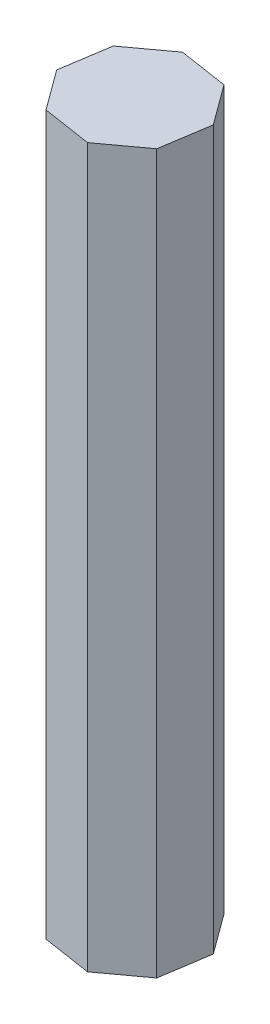
SolidWorks part; units mm, degrees
ref_plane "Front Plane" through (0, 0, 0) normal (0, 0, 1) x (1, 0, 0)
ref_plane "Top Plane" through (0, 0, 0) normal (0, 1, 0) x (1, 0, 0)
ref_plane "Right Plane" through (0, 0, 0) normal (1, 0, 0) x (0, 0, -1)
sketch "Sketch1" plane through (0, 0, 0) normal (0, 1, 0) x (1, 0, 0)
  line L1 (11.7493, -7.1357) -> (13.3537, 3.2623)
  line L2 (13.3537, 3.2623) -> (7.1357, 11.7493)
  line L3 (7.1357, 11.7493) -> (-3.2623, 13.3537)
  line L4 (-3.2623, 13.3537) -> (-11.7493, 7.1357)
  line L5 (-11.7493, 7.1357) -> (-13.3537, -3.2623)
  line L6 (-13.3537, -3.2623) -> (-7.1357, -11.7493)
  line L7 (-7.1357, -11.7493) -> (3.2623, -13.3537)
  line L8 (3.2623, -13.3537) -> (11.7493, -7.1357)
  circle A0 centre (0, 0) radius 12.7 construction
  dimension "D1" = 25.4
  dimension "D2" = 10.398
extrude "Boss-Extrude1" add sketch "Sketch1" against normal blind 152.4
